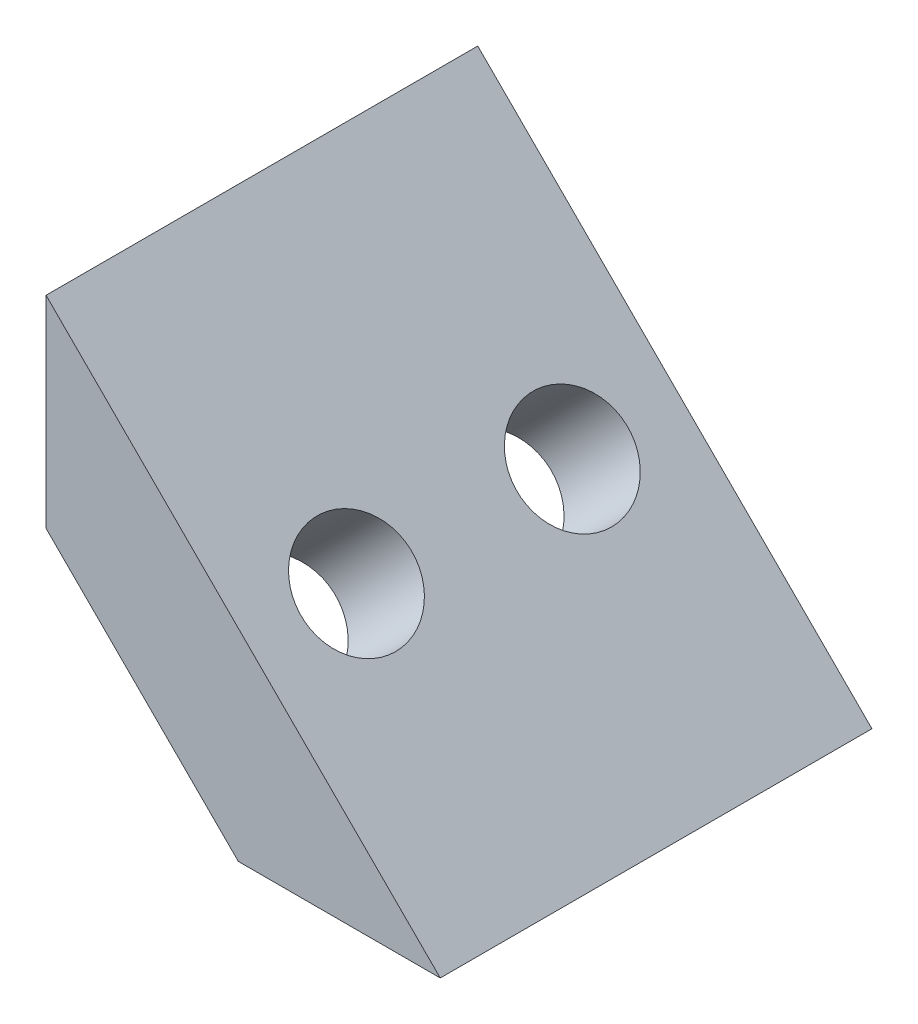
SolidWorks part; units mm, degrees
ref_plane "Front Plane" through (0, 0, 0) normal (0, 0, 1) x (1, 0, 0)
ref_plane "Top Plane" through (0, 0, 0) normal (0, 1, 0) x (1, 0, 0)
ref_plane "Right Plane" through (0, 0, 0) normal (1, 0, 0) x (0, 0, -1)
sketch "Sketch1" plane through (0, 0, 0) normal (0, 0, 1) x (1, 0, 0)
  line L0 (0, 11.5966) -> (11.5966, 0)
  line L1 (11.5966, 0) -> (5.6569, 0)
  line L2 (5.6569, 0) -> (0, 5.6569)
  line L3 (0, 5.6569) -> (0, 11.5966)
  dimension "D1" = 45
  dimension "D2" = 16.4
  dimension "D3" = 8
extrude "Boss-Extrude1" add sketch "Sketch1" along normal mid plane 12.7
ref_plane "Plane2" through (5.7983, 5.7983, 0) normal (0.7071, 0.7071, 0) x (0, 0, -1)
hole_wizard "CSK for #4 Flat Head Machine Screw (100)1" positions "Sketch4" profile "Sketch5" countersink size "#4" standard "ANSI Inch" end condition through all
sketch "Sketch4" plane through (2.8284, 2.8284, 0) normal (-0.7071, -0.7071, 0) x (0, 0, 1)
  line L0 (0, 5.5186) -> (0, -5.7006) construction
  line L3 (0, -0.2247) -> (-6.35, -0.2247) construction
  line L5 (-6.35, 4) -> (-6.35, -4) construction
  point P0 (-3.175, -0.2247)
  point P1 (3.175, -0.2247)
sketch "Sketch5" plane through (2.9873, 2.6695, -3.175) normal (0, 0, 1) x (0.7071, -0.7071, 0)
  line L0 (0, 0) -> (0, 12.4)
  line L1 (0, 12.4) -> (1.6319, 12.4)
  line L2 (1.6319, 12.4) -> (1.6319, 1.0284)
  line L3 (1.6319, 1.0284) -> (2.8575, 0)
  line L5 (2.8575, 0) -> (0, 0)
  line L6 (-1.6319, 1.0284) -> (-2.8575, 0) construction
  line L11 (0, -6.35) -> (0, 107.95) construction
  dimension "Thru Hole Dia." = 3.2639
  dimension "Thru Hole Depth" = 12.4
  dimension "Near C'Sink Dia." = 5.715
  dimension "Near C'Sink Angle" = 100
